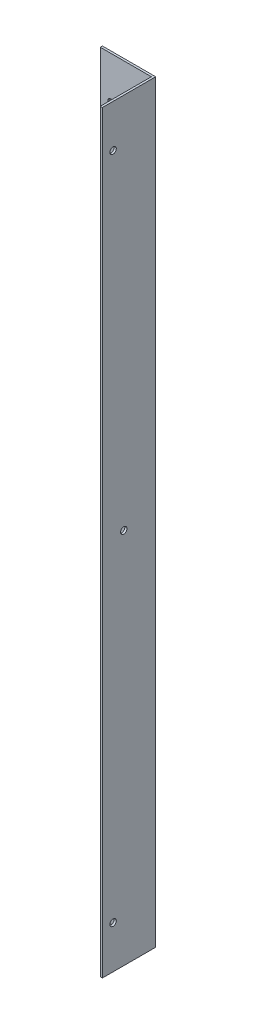
SolidWorks part; units mm, degrees
material "Plástico personalizado"
ref_plane "Alzado" through (0, 0, 0) normal (0, 0, 1) x (1, 0, 0)
ref_plane "Planta" through (0, 0, 0) normal (0, 1, 0) x (1, 0, 0)
ref_plane "Vista lateral" through (0, 0, 0) normal (1, 0, 0) x (0, 0, -1)
sketch "Croquis1" plane through (0, 0, 0) normal (0, 0, 1) x (1, 0, 0)
  line L0 (-56.2582, 65.1807) -> (-80.2582, 65.1807)
  line L1 (-80.2582, 65.1807) -> (-80.2582, -288.8193)
  line L4 (-56.2582, 65.1807) -> (-56.2582, -288.8193)
  line L5 (-56.2582, -288.8193) -> (-80.2582, -288.8193)
  circle A0 centre (-75.2582, 45.1807) radius 1.5
  circle A1 centre (-75.2582, -268.8193) radius 1.5
  dimension "D1" = 5
  dimension "D4" = 24
  dimension "D2" = 354
  dimension "D3" = 5
  dimension "D5" = 20
  dimension "D6" = 20
sketch "Croquis2" plane through (0, 0, 0) normal (0, 0, 1) x (1, 0, 0)
  line L1 (-56.2582, 65.1807) -> (-55.2582, 65.1807)
  line L2 (-56.2582, 65.1807) -> (-56.2582, -288.8193)
  line L3 (-56.2582, -288.8193) -> (-55.2582, -288.8193)
  line L4 (-55.2582, 65.1807) -> (-55.2582, -288.8193)
  dimension "D1" = 1
  dimension "D2" = 354
extrude "Saliente-Extruir2" add sketch "Croquis2" along normal blind 25
sketch "Croquis5" plane through (-55.2582, 0, 0) normal (1, 0, 0) x (0, 0, -1)
  line L0 (-25, 65.1807) -> (0, 65.1807) construction
  line L1 (-25, -288.8193) -> (0, -288.8193) construction
  line L2 (-25, -288.8193) -> (-25, 65.1807) construction
  line L3 (0, -288.8193) -> (0, 65.1807) construction
  circle A0 centre (-20, 45.1807) radius 1.5
  circle A1 centre (-20, -268.8193) radius 1.5
  circle A2 centre (-15, -111.8193) radius 1.5
  dimension "D1" = 20
  dimension "D4" = 5
  dimension "D5" = 15
  dimension "D2" = 20
  dimension "D3" = 5
  dimension "D6" = 177
extrude "Cortar-Extruir2" cut sketch "Croquis5" against normal blind 1
extrude "Saliente-Extruir3" add sketch "Croquis1" along normal blind 1
